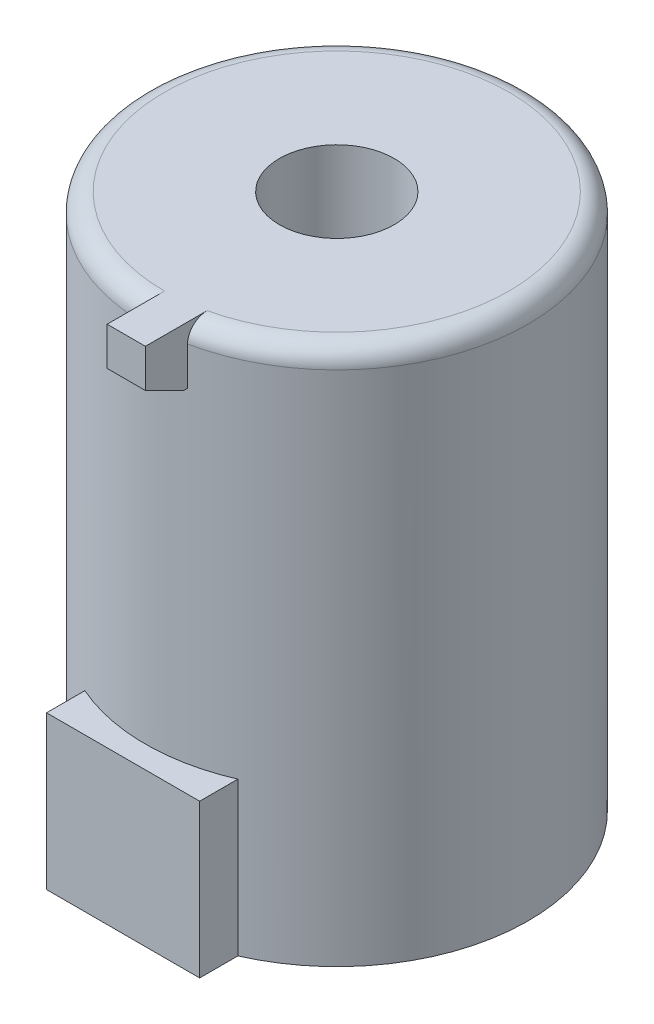
SolidWorks part; units mm, degrees
ref_plane "前基準面" through (0, 0, 0) normal (0, 0, 1) x (1, 0, 0)
ref_plane "上基準面" through (0, 0, 0) normal (0, 1, 0) x (1, 0, 0)
ref_plane "右基準面" through (0, 0, 0) normal (1, 0, 0) x (0, 0, -1)
sketch "草圖1" plane through (0, 0, 0) normal (0, 1, 0) x (1, 0, 0)
  circle A0 centre (0, 0) radius 50
  dimension "D1" = 100
extrude "填料-伸長1" add sketch "草圖1" along normal blind 140
sketch "草圖2" plane through (0, 0, 0) normal (0, -1, 0) x (1, 0, 0)
  line L0 (-20, -65.6591) -> (-20, 170.5003) construction
  line L1 (0, 0) -> (0, 63.8278) construction
  line L2 (-20, 45.8258) -> (20, 45.8258)
  line L3 (-20, 45.8258) -> (-20, 55.8258)
  line L4 (-20, 55.8258) -> (20, 55.8258)
  line L5 (20, 45.8258) -> (20, 55.8258)
  circle A0 centre (0, 0) radius 50 construction
  dimension "D1" = 20
  dimension "D2" = 40
  dimension "D3" = 10
extrude "填料-伸長2" add sketch "草圖2" against normal blind 40
sketch "草圖3" plane through (0, 140, 0) normal (0, 1, 0) x (1, 0, 0)
  circle A0 centre (0, 0) radius 15
  dimension "D1" = 30
extrude "除料-伸長1" cut sketch "草圖3" against normal blind 40
sketch "草圖4" plane through (0, 0, 0) normal (1, 0, 0) x (0, 0, -1)
  line L0 (-50, 140) -> (-60, 140)
  line L1 (50, 140) -> (-50, 140) construction
  line L2 (-60, 140) -> (-60, 130)
  line L3 (-60, 130) -> (-50, 125)
  line L4 (-50, 140) -> (-50, 40) construction
  line L5 (-50, 140) -> (-44.5876, 140)
  line L6 (-44.5876, 140) -> (-44.5876, 125)
  line L7 (-44.5876, 125) -> (-50, 125)
  dimension "D1" = 10
  dimension "D2" = 10
  dimension "D3" = 15
extrude "填料-伸長4" add sketch "草圖4" along normal blind 10
fillet "圓角2" radius 5 1 edges at (-5.0254, 140, -49.7468)
sketch "草圖5" plane through (0, 0, 0) normal (0, -1, 0) x (1, 0, 0)
  point P0 (0, 0)
